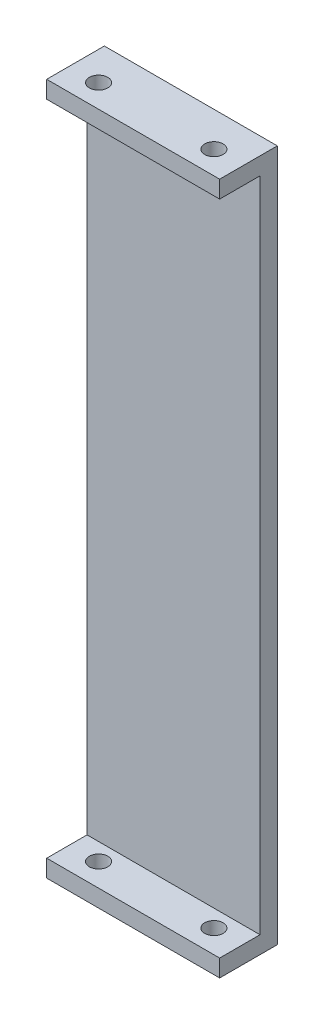
SolidWorks part; units mm, degrees
material "橡胶"
ref_plane "前视基准面" through (0, 0, 0) normal (0, 0, 1) x (1, 0, 0)
ref_plane "上视基准面" through (0, 0, 0) normal (0, 1, 0) x (1, 0, 0)
ref_plane "右视基准面" through (0, 0, 0) normal (1, 0, 0) x (0, 0, -1)
other "Configuration Table"
sketch "草图1" plane through (0, 0, 0) normal (0, 0, 1) x (1, 0, 0)
  line L1 (-10.0858, 114.268) -> (19.9142, 114.268)
  line L2 (-10.0858, 114.268) -> (-10.0858, -5.732)
  line L3 (-10.0858, -5.732) -> (19.9142, -5.732)
  line L4 (19.9142, 114.268) -> (19.9142, -5.732)
  dimension "D1" = 30
  dimension "D2" = 120
extrude "凸台-拉伸1" add sketch "草图1" along normal blind 10
sketch "草图2" plane through (0, 0, 10) normal (0, 0, 1) x (1, 0, 0)
  line L0 (-10.0858, 114.268) -> (-10.0858, -5.732) construction
  line L1 (-10.0858, -2.732) -> (19.9142, -2.732)
  line L2 (-10.0858, -2.732) -> (-10.0858, 111.268)
  line L3 (-10.0858, 111.268) -> (19.9142, 111.268)
  line L4 (19.9142, -2.732) -> (19.9142, 111.268)
  line L5 (19.9142, -5.732) -> (19.9142, 114.268) construction
  line L6 (19.9142, 114.268) -> (-10.0858, 114.268) construction
  line L7 (-10.0858, -5.732) -> (19.9142, -5.732) construction
  dimension "D1" = 3
  dimension "D2" = 3
extrude "切除-拉伸1" cut sketch "草图2" against normal blind 7
sketch "草图3" plane through (0, 114.268, 0) normal (0, 1, 0) x (1, 0, 0)
  line L0 (-10.0858, -6) -> (19.9142, -6) construction
  line L1 (-10.0858, -10) -> (-10.0858, 0) construction
  line L2 (19.9142, -10) -> (19.9142, 0) construction
  line L3 (19.9142, -10) -> (-10.0858, -10) construction
  line L4 (4.9142, 0) -> (4.9142, -10) construction
  line L5 (19.9142, 0) -> (-10.0858, 0) construction
  circle A0 centre (-5.0858, -6) radius 1.6
  circle A1 centre (14.9142, -6) radius 1.6
  dimension "D2" = 10
  dimension "D4" = 3.2
  dimension "D1" = 4
  dimension "D3" = 10
extrude "切除-拉伸2" cut sketch "草图3" against normal through all
